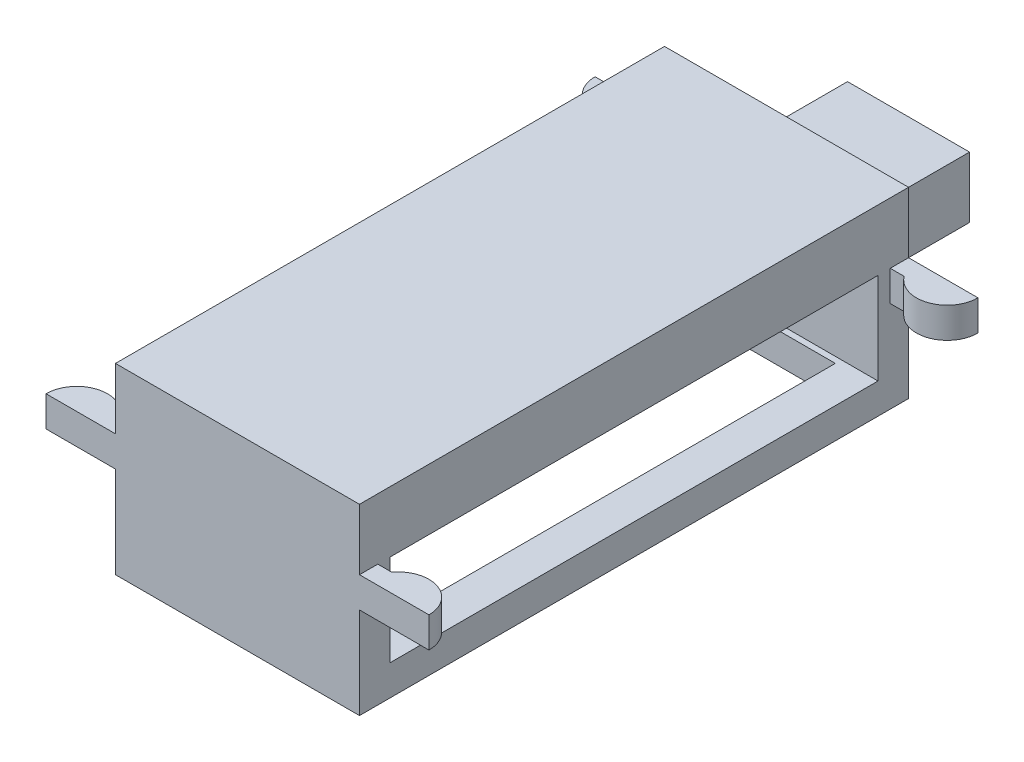
SolidWorks part; units mm, degrees
ref_plane "前视基准面" through (0, 0, 0) normal (0, 0, 1) x (1, 0, 0)
ref_plane "上视基准面" through (0, 0, 0) normal (0, 1, 0) x (1, 0, 0)
ref_plane "右视基准面" through (0, 0, 0) normal (1, 0, 0) x (0, 0, -1)
sketch "草图1" plane through (0, 0, 0) normal (0, 1, 0) x (1, 0, 0)
  line L1 (-2, 4) -> (2, 4)
  line L2 (-2, 4) -> (-2, -4)
  line L3 (-2, -4) -> (2, -4)
  line L4 (2, 4) -> (2, -4)
  line L5 (-2, 4) -> (2, -4) construction
  line L6 (-2, -4) -> (2, 4) construction
  point P0 (0, 0)
  dimension "D1" = 8
  dimension "D2" = 4
extrude "凸台-拉伸1" add sketch "草图1" along normal blind 1
sketch "草图2" plane through (0, 0, -4) normal (0, 0, -1) x (-1, 0, 0)
  line L0 (2, 1) -> (2, 0) construction
  line L1 (-2, 1) -> (2, 1)
  line L2 (-2, 1) -> (-2, -1.5)
  line L3 (-2, -1.5) -> (2, -1.5)
  line L4 (2, 1) -> (2, -1.5)
  dimension "D1" = 2.5
extrude "凸台-拉伸2" add sketch "草图2" along normal blind 0.5
mirror "镜向1" about plane through (0, 0, 0) normal (0, 0, 1) of "凸台-拉伸2"
sketch "草图3" plane through (0, -1.5, 0) normal (0, -1, 0) x (1, 0, 0)
  line L0 (-1.4, 3.9) -> (1.4, 3.9)
  line L1 (-2, 4.5) -> (2, 4.5)
  line L2 (-2, 4.5) -> (-2, -4.5)
  line L3 (-2, -4.5) -> (2, -4.5)
  line L4 (2, 4.5) -> (2, -4.5)
  line L5 (1.4, 3.9) -> (1.4, -3.9)
  line L6 (-1.4, -3.9) -> (1.4, -3.9)
  line L7 (-1.4, 3.9) -> (-1.4, -3.9)
  dimension "D1" = 0.6
extrude "凸台-拉伸3" add sketch "草图3" along normal blind 0.5
sketch "草图4" plane through (0, 0, 0) normal (0, 1, 0) x (1, 0, 0)
  line L1 (2, 4.5) -> (-2, 4.5) construction
  line L2 (-3.1386, -4.5) -> (-3.1386, -3.7574) construction
  line L3 (2, 4.5) -> (3.1386, 4.5)
  line L4 (-2, 4.5) -> (2, 4.5)
  line L5 (2, 4.5) -> (2.0018, 4.5159)
  line L6 (-2.2279, 4.2) -> (2.2279, 4.2)
  line L7 (3.1386, 4.5) -> (3.1386, 3.7574) construction
  line L8 (-3.1386, 4.5) -> (-3.1386, 3.7574) construction
  line L9 (-2, 4.5) -> (-2.0018, 4.5159)
  line L10 (-2, 4.5) -> (-3.1386, 4.5)
  line L11 (-2, 0) -> (2, 0) construction
  line L12 (-2, 4.5) -> (-2, -4.5) construction
  line L13 (2, -4.5) -> (2, 4.5) construction
  line L14 (3.1386, -4.5) -> (3.1386, -3.7574) construction
  line L15 (2, -4.5) -> (-2, -4.5) construction
  line L16 (-2, -4.5) -> (-3.1386, -4.5)
  line L17 (-2, -4.5) -> (-2.0018, -4.5159)
  line L18 (-2.2279, -4.2) -> (2.2279, -4.2)
  line L19 (2, -4.5) -> (2.0018, -4.5159)
  line L20 (-2, -4.5) -> (2, -4.5)
  line L21 (2, -4.5) -> (3.1386, -4.5)
  arc A0 (3.1386, 4.5) -> (2.2279, 4.2) centre (2.6339, 4.5) cw
  arc A1 (-3.1386, 4.5) -> (-2.2279, 4.2) centre (-2.6339, 4.5) ccw
  arc A2 (-3.1386, -4.5) -> (-2.2279, -4.2) centre (-2.6339, -4.5) cw
  arc A3 (3.1386, -4.5) -> (2.2279, -4.2) centre (2.6339, -4.5) ccw
  point P7 (0, 4.5)
  point P13 (0, 4.2)
  point P28 (0, 0)
  point P34 (0, -4.2)
  point P35 (0, -4.5)
  dimension "D1" = 0.3
extrude "凸台-拉伸4" add sketch "草图4" against normal blind 0.5 contours L10 A1 L6 A0 L3 L4 | L21 A3 L18 A2 L16 L20
sketch "草图5" plane through (0, 0, -4.5) normal (0, 0, -1) x (-1, 0, 0)
  line L1 (-1, 0) -> (1, 0)
  line L2 (-1, 0) -> (-1, -1)
  line L3 (-1, -1) -> (1, -1)
  line L4 (1, 0) -> (1, -1)
  dimension "D1" = 2
  dimension "D2" = 1
extrude "凸台-拉伸5" add sketch "草图5" along normal blind 2
